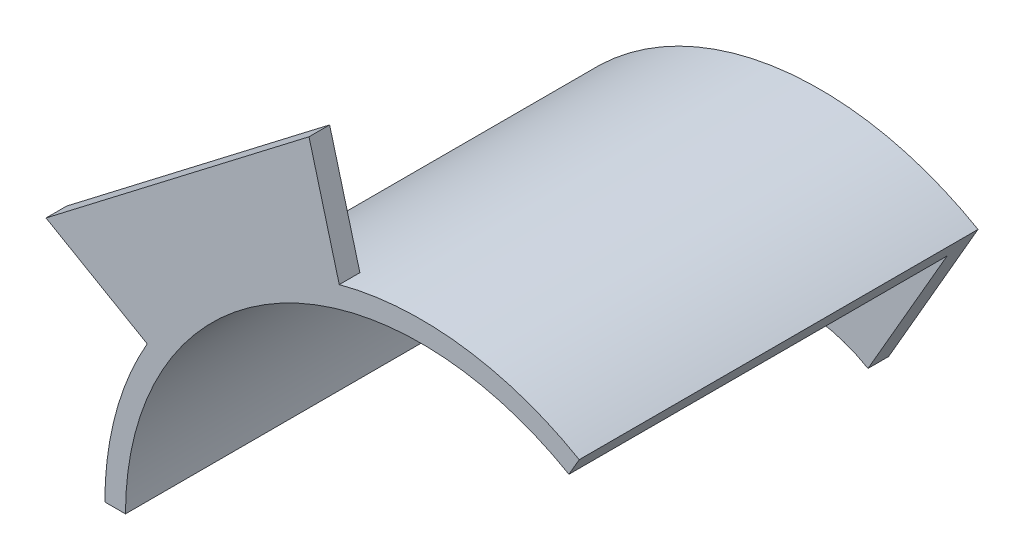
SolidWorks part; units mm, degrees
ref_plane "Front Plane" through (0, 0, 0) normal (0, 0, 1) x (1, 0, 0)
ref_plane "Top Plane" through (0, 0, 0) normal (0, 1, 0) x (1, 0, 0)
ref_plane "Right Plane" through (0, 0, 0) normal (1, 0, 0) x (0, 0, -1)
sketch "Sketch1" plane through (0, 0, 0) normal (0, 0, 1) x (1, 0, 0)
  line L0 (-122.2529, 0) -> (113.0578, 0) construction
  line L1 (0, 63.3207) -> (0, -71.8889) construction
  circle A0 centre (0, 0) radius 43
  circle A1 centre (0, 0) radius 46
  dimension "D1" = 86
extrude "Boss-Extrude1" add sketch "Sketch1" along normal blind 55 contours A0 | A1
ref_plane "Plane1" through (0, 0, 0) normal (0, 0, -1) x (-1, 0, 0)
sketch "Sketch2" plane through (0, 0, 0) normal (0, 0, -1) x (-1, 0, 0)
  line L0 (0, 0) -> (67.8196, 0) construction
  line L1 (0, 0) -> (-28.1852, 48.8181) construction
  line L2 (-10, 17.3205) -> (-23, 39.8372)
  line L3 (46, 0) -> (20, 0)
  arc A0 (-23, 39.8372) -> (46, 0) centre (0, 0) cw
  circle A1 centre (0, 0) radius 46 construction
  arc A2 (20, 0) -> (-10, 17.3205) centre (0, 0) ccw
  dimension "D2" = 40
  dimension "D1" = 120
extrude "Boss-Extrude2" add sketch "Sketch2" along normal blind 3
sketch "Sketch3" plane through (0, 0, -3) normal (0, 0, -1) x (-1, 0, 0)
  line L0 (-23, 39.8372) -> (-21.5, 37.2391)
  line L1 (43, 0) -> (46, 0)
  arc A0 (-23, 39.8372) -> (46, 0) centre (0, 0) ccw
  arc A1 (-21.5, 37.2391) -> (43, 0) centre (0, 0) ccw
extrude "Cut-Extrude1" cut sketch "Sketch3" against normal up to surface (58 mm away) up to face at (46, 0, 55)
ref_plane "Plane2" through (0, 0, 55) normal (0, 0, 1) x (1, 0, 0)
sketch "Sketch4" plane through (0, 0, 55) normal (0, 0, 1) x (1, 0, 0)
  line L0 (0, 0) -> (-132.4127, 0) construction
  line L1 (0, 0) -> (-112.8632, 65.1616) construction
  line L2 (0, 0) -> (-20.2598, 75.6107) construction
  line L3 (-37.2391, 21.5) -> (-54.5596, 31.5)
  line L4 (-11.1292, 41.5348) -> (-16.3056, 60.8533)
  line L5 (-54.5596, 31.5) -> (-16.3056, 60.8533)
  arc A0 (21.5, 37.2391) -> (-43, 0) centre (0, 0) ccw construction
  arc A1 (21.5, 37.2391) -> (-43, 0) centre (0, 0) ccw construction
  arc A2 (-37.2391, 21.5) -> (-11.1292, 41.5348) centre (0, 0) cw
  dimension "D1" = 30
  dimension "D2" = 45
  dimension "D3" = 20
  dimension "D4" = 20
extrude "Boss-Extrude3" add sketch "Sketch4" against normal blind 3
